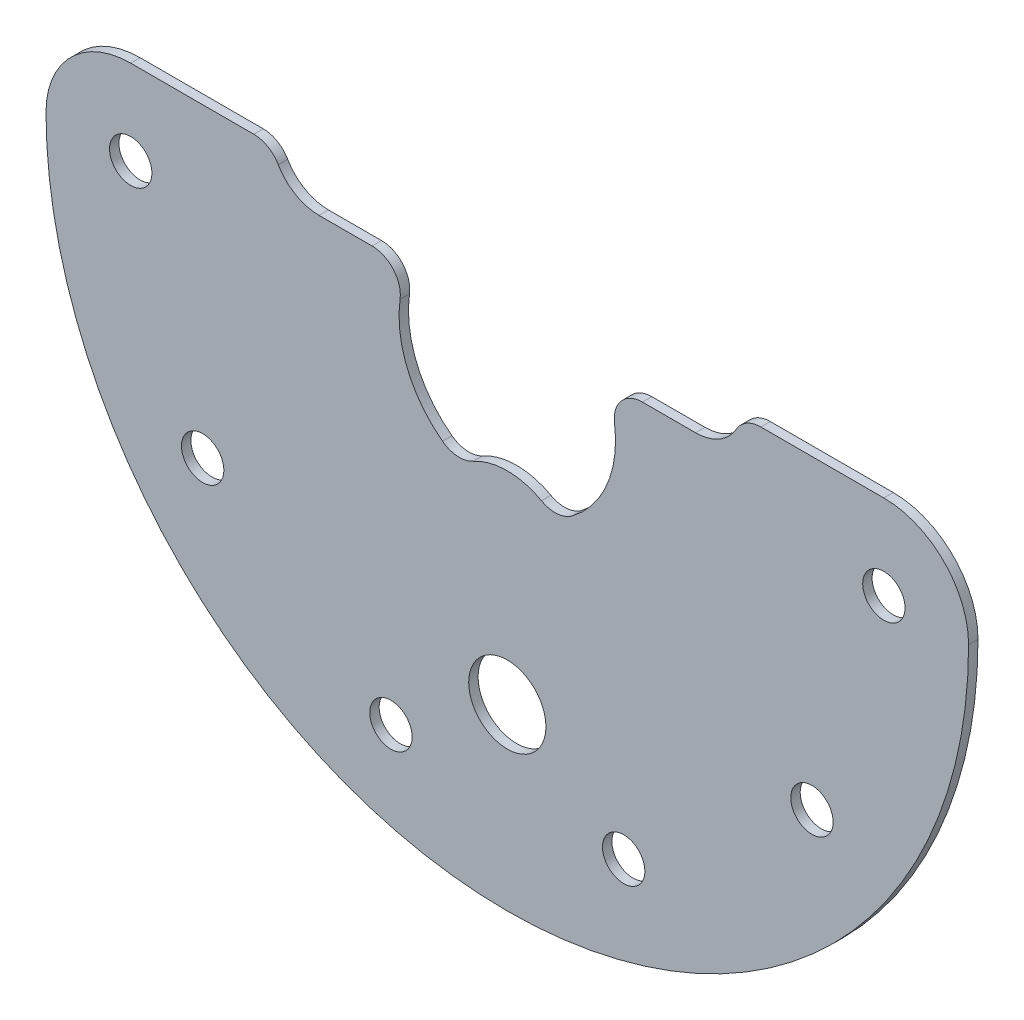
SolidWorks part; units mm, degrees
ref_plane "前视基准面" through (0, 0, 0) normal (0, 0, 1) x (1, 0, 0)
ref_plane "上视基准面" through (0, 0, 0) normal (0, 1, 0) x (1, 0, 0)
ref_plane "右视基准面" through (0, 0, 0) normal (1, 0, 0) x (0, 0, -1)
ref_plane "基准面4" through (0, 0, 1) normal (0, 0, 1) x (1, 0, 0)
sketch "草图1" plane through (0, 0, 1) normal (0, 0, 1) x (1, 0, 0)
  line L0 (-614.3614, 5) -> (-620, 5)
  line L1 (-626.9282, 9) -> (-640, 9)
  line L2 (-560, 9) -> (-573.0718, 9)
  line L3 (-580, 5) -> (-585.6386, 5)
  circle A0 centre (-640, 0) radius 2.25
  arc A1 (-606.8774, -9.2169) -> (-611.3901, 1.5862) centre (-600, 0) cw
  arc A2 (-611.3901, 1.5862) -> (-614.3614, 5) centre (-614.3614, 2) ccw
  arc A3 (-620, 5) -> (-624.3301, 7.5) centre (-620, 10) cw
  arc A4 (-624.3301, 7.5) -> (-626.9282, 9) centre (-626.9282, 6) ccw
  arc A5 (-640, 9) -> (-649, 0) centre (-640, 0) ccw
  arc A6 (-649, 0) -> (-551, 0) centre (-600, 0) ccw
  arc A7 (-551, 0) -> (-560, 9) centre (-560, 0) ccw
  arc A8 (-573.0718, 9) -> (-575.6699, 7.5) centre (-573.0718, 6) ccw
  arc A9 (-575.6699, 7.5) -> (-580, 5) centre (-580, 10) cw
  arc A10 (-585.6386, 5) -> (-588.6099, 1.5862) centre (-585.6386, 2) ccw
  arc A11 (-588.6099, 1.5862) -> (-593.1226, -9.2169) centre (-600, 0) cw
  arc A12 (-593.1226, -9.2169) -> (-596.3691, -9.4375) centre (-594.9167, -6.8125) cw
  arc A13 (-596.3691, -9.4375) -> (-603.6309, -9.4375) centre (-600, -16) ccw
  arc A14 (-603.6309, -9.4375) -> (-606.8774, -9.2169) centre (-605.0833, -6.8125) cw
  circle A15 centre (-600, -30) radius 4.1
  circle A16 centre (-567.6393, -23.5114) radius 2.25
  circle A17 centre (-587.6393, -38.0423) radius 2.25
  circle A18 centre (-612.3607, -38.0423) radius 2.25
  circle A19 centre (-632.3607, -23.5114) radius 2.25
  circle A20 centre (-560, 0) radius 2.25
extrude "凸台-拉伸1" add sketch "草图1" against normal blind 1
